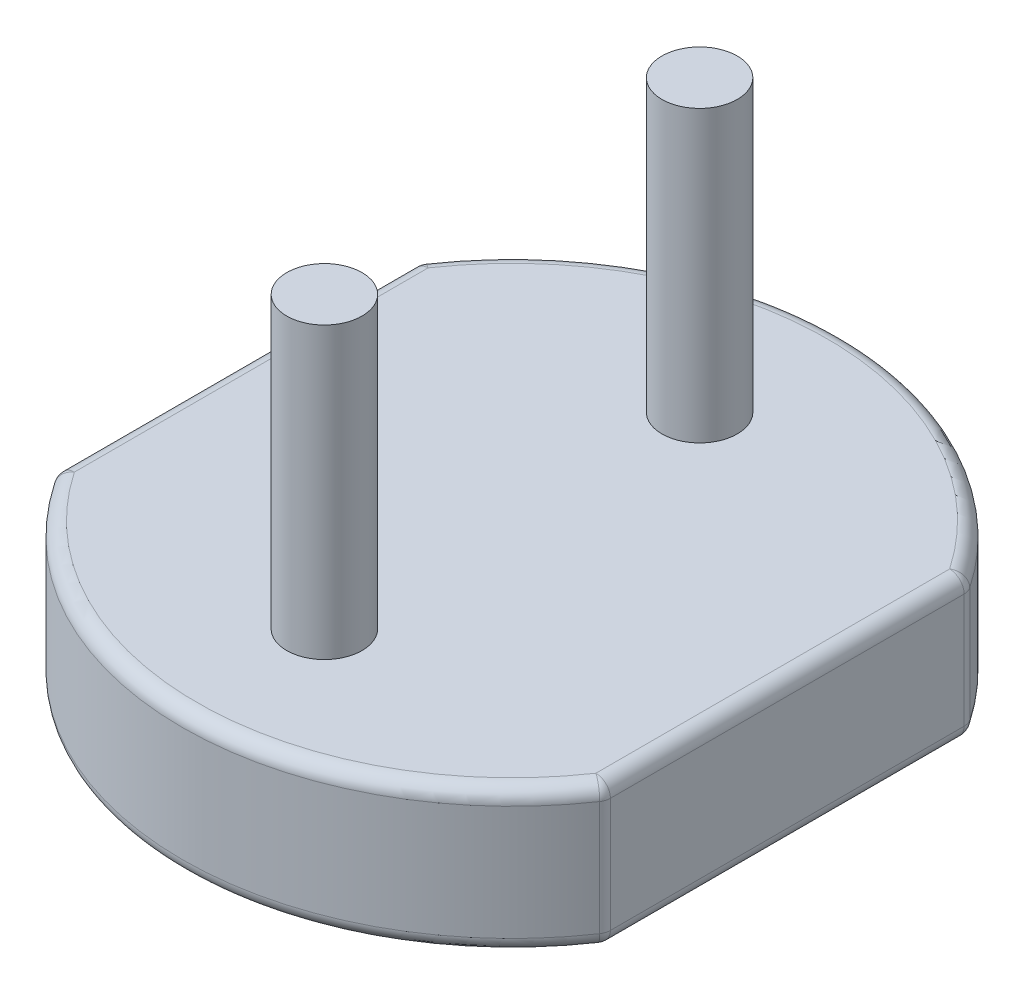
SolidWorks part; units mm, degrees
material "1060 Alloy"
ref_plane "Front Plane" through (0, 0, 0) normal (0, 0, 1) x (1, 0, 0)
ref_plane "Top Plane" through (0, 0, 0) normal (0, 1, 0) x (1, 0, 0)
ref_plane "Right Plane" through (0, 0, 0) normal (1, 0, 0) x (0, 0, -1)
sketch "Sketch1" plane through (0, 0, 0) normal (0, 1, 0) x (1, 0, 0)
  line L0 (-1.9, 1.2512) -> (-1.9, -1.2512)
  line L1 (1.9, 1.2512) -> (1.9, -1.2512)
  line L2 (-1.9, 1.2512) -> (1.9, 1.2512) construction
  line L3 (-1.9, -1.2512) -> (1.9, -1.2512) construction
  arc A0 (-1.9, -1.2512) -> (1.9, -1.2512) centre (0, 0) ccw
  arc A1 (1.9, 1.2512) -> (-1.9, 1.2512) centre (0, 0) ccw
  dimension "D1" = 4.55
  dimension "D2" = 3.8
extrude "Boss-Extrude1" add sketch "Sketch1" along normal blind 1
sketch "Sketch2" plane through (0, 1, 0) normal (0, 1, 0) x (1, 0, 0)
  line L0 (0, 0) -> (0, 1.295) construction
  line L1 (0, 0) -> (0, -1.295) construction
  circle A0 centre (0, 1.295) radius 0.26
  circle A1 centre (0, -1.295) radius 0.26
  dimension "D1" = 0.52
  dimension "D2" = 2.59
extrude "Boss-Extrude2" add sketch "Sketch2" along normal blind 10 and the other way blind 1.1
sketch "Sketch4" plane through (0, 0, 0) normal (0, -1, 0) x (1, 0, 0)
  line L0 (1.9, -1.2512) -> (1.9, 1.2512)
  line L1 (-1.9, 1.2512) -> (-1.9, -1.2512)
  line L2 (-1.4, 1.0912) -> (-1.4, -1.0912)
  line L3 (1.4, -1.0912) -> (1.4, 1.0912)
  line L4 (1.35, 1.1524) -> (1.35, -1)
  line L5 (1.05, -1) -> (1.05, 0.9)
  line L6 (0.75, 0.9) -> (0.75, -0.9)
  line L7 (0.45, -0.9) -> (0.45, 0.7)
  line L8 (0.15, 0.7) -> (0.15, -0.75)
  line L9 (0, 0) -> (0, -2.9017) construction
  line L10 (1.35, -1) -> (1.05, -1) construction
  line L11 (0, -0.9) -> (-0.3797, -0.9) construction
  line L12 (0.75, -0.9) -> (0.45, -0.9) construction
  line L13 (1.25, 1.1524) -> (1.25, -1)
  line L14 (1.15, -1) -> (1.15, 0.9)
  line L15 (0.65, 0.9) -> (0.65, -0.9)
  line L16 (0.55, -0.9) -> (0.55, 0.7)
  line L17 (0.05, 0.7) -> (0.05, -0.75)
  line L18 (1.25, 1.1524) -> (1.25, 1.2602)
  line L19 (-1.25, 1.1524) -> (-1.25, 1.2602)
  line L20 (-1.35, 1.1524) -> (-1.35, -1)
  line L21 (-1.25, 1.1524) -> (-1.25, -1)
  line L22 (-1.15, -1) -> (-1.15, 0.9)
  line L23 (-1.05, -1) -> (-1.05, 0.9)
  line L24 (-0.75, 0.9) -> (-0.75, -0.9)
  line L25 (-0.65, 0.9) -> (-0.65, -0.9)
  line L26 (-0.55, -0.9) -> (-0.55, 0.7)
  line L27 (-0.45, -0.9) -> (-0.45, 0.7)
  line L28 (-0.15, 0.7) -> (-0.15, -0.75)
  line L29 (-0.05, 0.7) -> (-0.05, -0.75)
  arc A0 (1.9, -1.2512) -> (-1.9, -1.2512) centre (0, 0) cw
  arc A1 (1.9, 1.2512) -> (-1.9, 1.2512) centre (0, 0) ccw
  arc A2 (-1.9, -1.2512) -> (1.9, -1.2512) centre (0, 0) ccw construction
  arc A3 (1.9, 1.2512) -> (-1.9, 1.2512) centre (0, 0) ccw construction
  arc A4 (1.4, -1.0912) -> (-1.4, -1.0912) centre (0, 0) cw
  arc A5 (1.4, 1.0912) -> (1.35, 1.1524) centre (0, 0) ccw
  arc A6 (1.35, -1) -> (1.05, -1) centre (1.2, -1) cw
  arc A7 (1.05, 0.9) -> (0.75, 0.9) centre (0.9, 0.9) ccw
  arc A8 (0.75, -0.9) -> (0.45, -0.9) centre (0.6, -0.9) cw
  arc A9 (0.45, 0.7) -> (0.15, 0.7) centre (0.3, 0.7) ccw
  arc A10 (0.15, -0.75) -> (-0.15, -0.75) centre (0, -0.75) cw
  arc A11 (1.25, -1) -> (1.15, -1) centre (1.2, -1) cw
  arc A12 (1.15, 0.9) -> (0.65, 0.9) centre (0.9, 0.9) ccw
  arc A13 (0.65, -0.9) -> (0.55, -0.9) centre (0.6, -0.9) cw
  arc A14 (0.55, 0.7) -> (0.05, 0.7) centre (0.3, 0.7) ccw
  arc A15 (0.05, -0.75) -> (0, -0.8) centre (0, -0.75) cw
  arc A16 (0.15, -0.75) -> (0, -0.9) centre (0, -0.75) cw construction
  arc A17 (1.25, 1.2602) -> (-1.25, 1.2602) centre (0, 0) ccw
  arc A18 (-1.25, -1) -> (-1.15, -1) centre (-1.2, -1) ccw
  arc A19 (1.4, 1.0912) -> (-1.4, 1.0912) centre (0, 0) ccw construction
  arc A20 (-1.35, -1) -> (-1.05, -1) centre (-1.2, -1) ccw
  arc A21 (-0.05, -0.75) -> (0, -0.8) centre (0, -0.75) ccw
  arc A22 (-0.65, -0.9) -> (-0.55, -0.9) centre (-0.6, -0.9) ccw
  arc A23 (-0.75, -0.9) -> (-0.45, -0.9) centre (-0.6, -0.9) ccw
  arc A24 (-1.05, 0.9) -> (-0.75, 0.9) centre (-0.9, 0.9) cw
  arc A25 (-1.15, 0.9) -> (-0.65, 0.9) centre (-0.9, 0.9) cw
  arc A26 (-0.55, 0.7) -> (-0.05, 0.7) centre (-0.3, 0.7) cw
  arc A27 (-0.45, 0.7) -> (-0.15, 0.7) centre (-0.3, 0.7) cw
  arc A28 (-1.35, 1.1524) -> (-1.4, 1.0912) centre (0, 0) ccw
  dimension "D2" = 0.3
  dimension "D4" = 0.1
  dimension "D5" = 0.8
  dimension "D6" = 1.45
  dimension "D7" = 1.6
  dimension "D8" = 1.8
  dimension "D9" = 1.9
  dimension "D1" = 0.5
  dimension "D3" = 0.1
extrude "Cut-Extrude1" cut sketch "Sketch4" against normal blind 0.01
fillet "Fillet1" radius 0.1 12 edges at (0, 1, 2.275) (-1.9, 1, 0) (-1.9, 0.505, 1.2512) (-1.9, 0.505, -1.2512) (1.9, 0.505, 1.2512) (1.9, 0.505, -1.2512) (-1.9, 0.01, 0) (0, 0.01, 2.275) (1.9, 0.01, 0) (0, 1, -2.275) (1.9, 1, 0) (0, 0.01, -2.275)
sketch "Sketch5" plane through (0, 11, 0) normal (0, 1, 0) x (1, 0, 0)
  circle A0 centre (0, 1.295) radius 0.26 construction
  point P0 (0.26, 1.295)
ref_plane "Plane1" through (1.9949, 0.3242, 0) normal (0.9871, 0.1604, 0) x (0, 0, -1)
sketch "Schizzo1" plane through (0, 11, 0) normal (0, 1, 0) x (1, 0, 0)
  circle A0 centre (0, 1.295) radius 0.26
  circle A1 centre (0, -1.295) radius 0.26
extrude "Taglio-Estrusione1" cut sketch "Schizzo1" against normal blind 8
